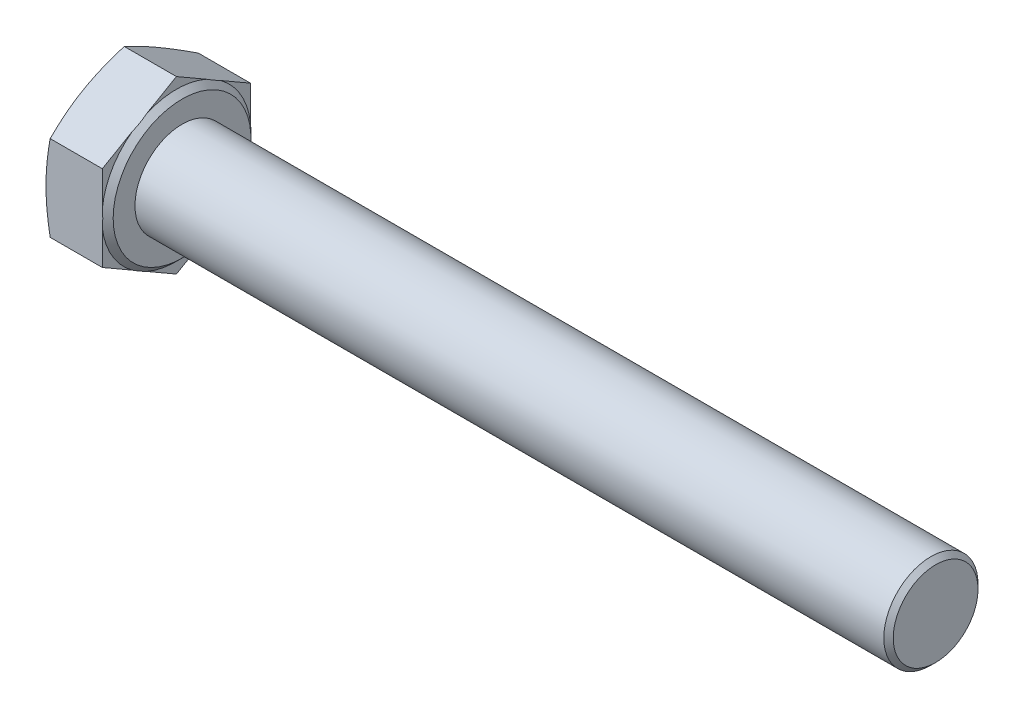
SolidWorks part; units mm, degrees
ref_plane "Front" through (0, 0, 0) normal (0, 0, 1) x (1, 0, 0)
ref_plane "Top" through (0, 0, 0) normal (0, 1, 0) x (1, 0, 0)
ref_plane "Right" through (0, 0, 0) normal (1, 0, 0) x (0, 0, -1)
sketch "Sketch2" plane through (0, 0, 0) normal (1, 0, 0) x (0, 0, -1)
  line L1 (7.865, -4.5409) -> (7.865, 4.5409)
  line L2 (7.865, 4.5409) -> (0, 9.0817)
  line L3 (0, 9.0817) -> (-7.865, 4.5409)
  line L4 (-7.865, 4.5409) -> (-7.865, -4.5409)
  line L5 (-7.865, -4.5409) -> (0, -9.0817)
  line L6 (0, -9.0817) -> (7.865, -4.5409)
  circle A0 centre (0, 0) radius 7.865 construction
  dimension "s" = 15.73
extrude "BaseHead" add sketch "Sketch2" along normal blind 6.58
sketch "Sketch3" plane through (0, 0, 0) normal (0, 0, 1) x (1, 0, 0)
  line L0 (6.58, 9.0817) -> (6.58, 7.315)
  line L2 (6.58, 7.315) -> (5.98, 7.915)
  line L3 (5.98, 7.915) -> (5.98, 9.0817)
  line L5 (5.98, 9.0817) -> (6.58, 9.0817)
  line L6 (-0.9571, 0) -> (7.6478, 0) construction
  line L7 (6.58, 9.0817) -> (0, 9.0817) construction
  dimension "D1" = 45
  dimension "c" = 0.6
  dimension "Dw" = 14.63
revolve "BearingFace" cut sketch "Sketch3" angle 360 about L6
sketch "Sketch4" plane through (0, 0, 0) normal (0, 0, 1) x (1, 0, 0)
  line L0 (-0.4935, 0) -> (3.5626, 0) construction
  line L2 (0, 9.0817) -> (0.4428, 9.0817)
  line L4 (0.4428, 9.0817) -> (0, 7.865)
  line L6 (0, 7.865) -> (0, 9.0817)
  line L7 (5.98, 9.0817) -> (0, 9.0817) construction
  dimension "D1" = 20
  dimension "D2" = 15.73
revolve "HeadChamfer" cut sketch "Sketch4" angle 360 about L0
sketch "Sketch5" plane through (6.58, 0, 0) normal (1, 0, 0) x (0, 0, -1)
  circle A0 centre (0, 0) radius 5
  dimension "d" = 10
extrude "BaseBody" add sketch "Sketch5" along normal blind 80
cosmetic thread "ThreadCosmetic1" [suppressed] parameters "D2"=8.376
chamfer "Chamfer1" distance 0.5 angle 45 1 edges at (86.58, 0, -5)
fillet "HeadFillet" [suppressed] radius 0.4
sketch "Sketch6" plane through (0, 0, 0) normal (0, 0, 1) x (1, 0, 0)
  line L0 (6.58, 5.812) -> (7.392, 5.812)
  line L1 (7.392, 5.812) -> (7.392, 5)
  line L2 (7.392, 5) -> (6.986, 4.2968)
  line L3 (6.986, 4.2968) -> (6.58, 5)
  line L4 (6.58, 5) -> (6.58, 5.812)
  line L5 (86.08, 5) -> (6.58, 5) construction
  line L6 (6.58, -7.315) -> (6.58, 7.315) construction
  dimension "D1" = 0.812
revolve "Cut-Revolve10" [suppressed] cut sketch "Sketch6" angle 360 about axis through (-0.9571, 0, 0) along (1, 0, 0)
pattern_linear "LPattern10" [suppressed] count 82
equation "\"D2@Sketch4\" = \"s@Sketch2\""
equation "\"D1@Chamfer1\" = 0.05 * \"d@Sketch5\""
equation "\"D1@Sketch6\" =  ( \"d@Sketch5\" - \"D2@ThreadCosmetic1\" )  / 2"
equation "\"pitch@LPattern10\" = \"D1@Sketch6\" * 1.2"
equation "\"D1@LPattern10\" = \"l@BaseBody\" / \"pitch@LPattern10\""
